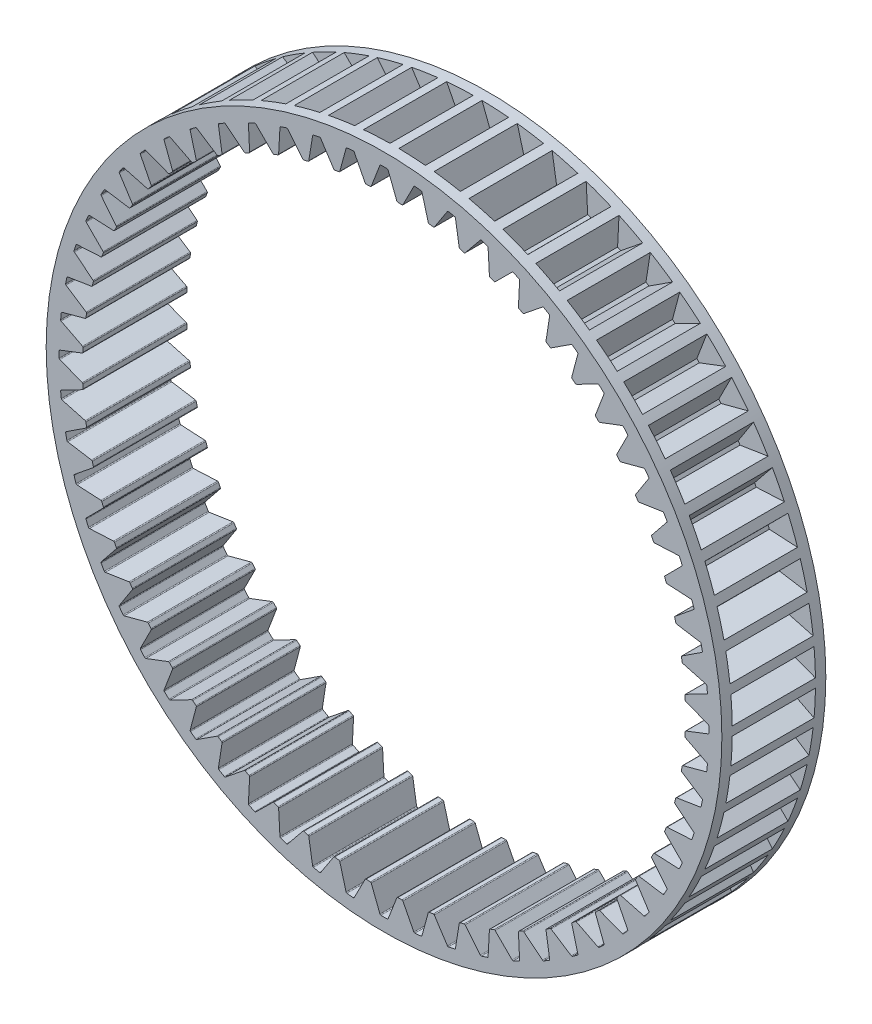
SolidWorks part; units mm, degrees
ref_plane "Front Plane" through (0, 0, 0) normal (0, 0, 1) x (1, 0, 0)
ref_plane "Top Plane" through (0, 0, 0) normal (0, 1, 0) x (1, 0, 0)
ref_plane "Right Plane" through (0, 0, 0) normal (1, 0, 0) x (0, 0, -1)
sketch "Sketch1" plane through (0, 0, 0) normal (0, 0, 1) x (1, 0, 0)
  line L0 (0, 0) -> (0, 31.25) construction
  line L1 (-1.2264, 29.034) -> (-0.3944, 31.1846)
  line L2 (1.2264, 29.034) -> (0.3944, 31.1846)
  line L3 (1.8152, 29.0031) -> (2.8674, 31.055)
  line L4 (4.2546, 28.7467) -> (3.6519, 30.9726)
  line L5 (4.8369, 28.6545) -> (6.0979, 30.5852)
  line L6 (7.2361, 28.1445) -> (6.8694, 30.4212)
  line L7 (7.8056, 27.9919) -> (9.2615, 29.7802)
  line L8 (10.1384, 27.234) -> (10.0117, 29.5365)
  line L9 (10.6888, 27.0227) -> (12.3236, 28.649)
  line L10 (12.9296, 26.025) -> (13.0442, 28.3282)
  line L11 (13.4549, 25.7574) -> (15.2507, 27.2039)
  line L12 (15.5791, 24.531) -> (15.9339, 26.8095)
  line L13 (16.0735, 24.2099) -> (18.0108, 25.4607)
  line L14 (18.0579, 22.7681) -> (18.6489, 24.9971)
  line L15 (18.5161, 22.3971) -> (20.5735, 23.4386)
  line L16 (20.3389, 20.7558) -> (21.1597, 22.9108)
  line L17 (20.7558, 20.3389) -> (22.9108, 21.1597)
  line L18 (22.3971, 18.5161) -> (23.4386, 20.5735)
  line L19 (22.7681, 18.0579) -> (24.9971, 18.6489)
  line L20 (24.2099, 16.0735) -> (25.4607, 18.0108)
  line L21 (24.531, 15.5791) -> (26.8095, 15.9339)
  line L22 (25.7574, 13.4549) -> (27.2039, 15.2507)
  line L23 (26.025, 12.9296) -> (28.3282, 13.0442)
  line L24 (27.0227, 10.6888) -> (28.649, 12.3236)
  line L25 (27.234, 10.1384) -> (29.5365, 10.0117)
  line L26 (27.9919, 7.8056) -> (29.7802, 9.2615)
  line L27 (28.1445, 7.2361) -> (30.4212, 6.8694)
  line L28 (28.6545, 4.8369) -> (30.5852, 6.0979)
  line L29 (28.7467, 4.2546) -> (30.9726, 3.6519)
  line L30 (29.0031, 1.8152) -> (31.055, 2.8674)
  line L31 (29.034, 1.2264) -> (31.1846, 0.3944)
  line L32 (29.034, -1.2264) -> (31.1846, -0.3944)
  line L33 (29.0031, -1.8152) -> (31.055, -2.8674)
  line L34 (28.7467, -4.2546) -> (30.9726, -3.6519)
  line L35 (28.6545, -4.8369) -> (30.5852, -6.0979)
  line L36 (28.1445, -7.2361) -> (30.4212, -6.8694)
  line L37 (27.9919, -7.8056) -> (29.7802, -9.2615)
  line L38 (27.234, -10.1384) -> (29.5365, -10.0117)
  line L39 (27.0227, -10.6888) -> (28.649, -12.3236)
  line L40 (26.025, -12.9296) -> (28.3282, -13.0442)
  line L41 (25.7574, -13.4549) -> (27.2039, -15.2507)
  line L42 (24.531, -15.5791) -> (26.8095, -15.9339)
  line L43 (24.2099, -16.0735) -> (25.4607, -18.0108)
  line L44 (22.7681, -18.0579) -> (24.9971, -18.6489)
  line L45 (22.3971, -18.5161) -> (23.4386, -20.5735)
  line L46 (20.7558, -20.3389) -> (22.9108, -21.1597)
  line L47 (20.3389, -20.7558) -> (21.1597, -22.9108)
  line L48 (18.5161, -22.3971) -> (20.5735, -23.4386)
  line L49 (18.0579, -22.7681) -> (18.6489, -24.9971)
  line L50 (16.0735, -24.2099) -> (18.0108, -25.4607)
  line L51 (15.5791, -24.531) -> (15.9339, -26.8095)
  line L52 (13.4549, -25.7574) -> (15.2507, -27.2039)
  line L53 (12.9296, -26.025) -> (13.0442, -28.3282)
  line L54 (10.6888, -27.0227) -> (12.3236, -28.649)
  line L55 (10.1384, -27.234) -> (10.0117, -29.5365)
  line L56 (7.8056, -27.9919) -> (9.2615, -29.7802)
  line L57 (7.2361, -28.1445) -> (6.8694, -30.4212)
  line L58 (4.8369, -28.6545) -> (6.0979, -30.5852)
  line L59 (4.2546, -28.7467) -> (3.6519, -30.9726)
  line L60 (1.8152, -29.0031) -> (2.8674, -31.055)
  line L61 (1.2264, -29.034) -> (0.3944, -31.1846)
  line L62 (-1.2264, -29.034) -> (-0.3944, -31.1846)
  line L63 (-1.8152, -29.0031) -> (-2.8674, -31.055)
  line L64 (-4.2546, -28.7467) -> (-3.6519, -30.9726)
  line L65 (-4.8369, -28.6545) -> (-6.0979, -30.5852)
  line L66 (-7.2361, -28.1445) -> (-6.8694, -30.4212)
  line L67 (-7.8056, -27.9919) -> (-9.2615, -29.7802)
  line L68 (-10.1384, -27.234) -> (-10.0117, -29.5365)
  line L69 (-10.6888, -27.0227) -> (-12.3236, -28.649)
  line L70 (-12.9296, -26.025) -> (-13.0442, -28.3282)
  line L71 (-13.4549, -25.7574) -> (-15.2507, -27.2039)
  line L72 (-15.5791, -24.531) -> (-15.9339, -26.8095)
  line L73 (-16.0735, -24.2099) -> (-18.0108, -25.4607)
  line L74 (-18.0579, -22.7681) -> (-18.6489, -24.9971)
  line L75 (-18.5161, -22.3971) -> (-20.5735, -23.4386)
  line L76 (-20.3389, -20.7558) -> (-21.1597, -22.9108)
  line L77 (-20.7558, -20.3389) -> (-22.9108, -21.1597)
  line L78 (-22.3971, -18.5161) -> (-23.4386, -20.5735)
  line L79 (-22.7681, -18.0579) -> (-24.9971, -18.6489)
  line L80 (-24.2099, -16.0735) -> (-25.4607, -18.0108)
  line L81 (-24.531, -15.5791) -> (-26.8095, -15.9339)
  line L82 (-25.7574, -13.4549) -> (-27.2039, -15.2507)
  line L83 (-26.025, -12.9296) -> (-28.3282, -13.0442)
  line L84 (-27.0227, -10.6888) -> (-28.649, -12.3236)
  line L85 (-27.234, -10.1384) -> (-29.5365, -10.0117)
  line L86 (-27.9919, -7.8056) -> (-29.7802, -9.2615)
  line L87 (-28.1445, -7.2361) -> (-30.4212, -6.8694)
  line L88 (-28.6545, -4.8369) -> (-30.5852, -6.0979)
  line L89 (-28.7467, -4.2546) -> (-30.9726, -3.6519)
  line L90 (-29.0031, -1.8152) -> (-31.055, -2.8674)
  line L91 (-29.034, -1.2264) -> (-31.1846, -0.3944)
  line L92 (-29.034, 1.2264) -> (-31.1846, 0.3944)
  line L93 (-29.0031, 1.8152) -> (-31.055, 2.8674)
  line L94 (-28.7467, 4.2546) -> (-30.9726, 3.6519)
  line L95 (-28.6545, 4.8369) -> (-30.5852, 6.0979)
  line L96 (-28.1445, 7.2361) -> (-30.4212, 6.8694)
  line L97 (-27.9919, 7.8056) -> (-29.7802, 9.2615)
  line L98 (-27.234, 10.1384) -> (-29.5365, 10.0117)
  line L99 (-27.0227, 10.6888) -> (-28.649, 12.3236)
  line L100 (-26.025, 12.9296) -> (-28.3282, 13.0442)
  line L101 (-25.7574, 13.4549) -> (-27.2039, 15.2507)
  line L102 (-24.531, 15.5791) -> (-26.8095, 15.9339)
  line L103 (-24.2099, 16.0735) -> (-25.4607, 18.0108)
  line L104 (-22.7681, 18.0579) -> (-24.9971, 18.6489)
  line L105 (-22.3971, 18.5161) -> (-23.4386, 20.5735)
  line L106 (-20.7558, 20.3389) -> (-22.9108, 21.1597)
  line L107 (-20.3389, 20.7558) -> (-21.1597, 22.9108)
  line L108 (-18.5161, 22.3971) -> (-20.5735, 23.4386)
  line L109 (-18.0579, 22.7681) -> (-18.6489, 24.9971)
  line L110 (-16.0735, 24.2099) -> (-18.0108, 25.4607)
  line L111 (-15.5791, 24.531) -> (-15.9339, 26.8095)
  line L112 (-13.4549, 25.7574) -> (-15.2507, 27.2039)
  line L113 (-12.9296, 26.025) -> (-13.0442, 28.3282)
  line L114 (-10.6888, 27.0227) -> (-12.3236, 28.649)
  line L115 (-10.1384, 27.234) -> (-10.0117, 29.5365)
  line L116 (-7.8056, 27.9919) -> (-9.2615, 29.7802)
  line L117 (-7.2361, 28.1445) -> (-6.8694, 30.4212)
  line L118 (-4.8369, 28.6545) -> (-6.0979, 30.5852)
  line L119 (-4.2546, 28.7467) -> (-3.6519, 30.9726)
  line L120 (-1.8152, 29.0031) -> (-2.8674, 31.055)
  arc A1 (-1.3152, 28.9702) -> (-1.7203, 28.9489) centre (0, 0) ccw
  arc A2 (0.3021, 31.2485) -> (-0.3021, 31.2485) centre (0, 0) ccw
  circle A3 centre (0, 0) radius 32.5
  arc A4 (-1.2264, 29.034) -> (-1.3152, 28.9702) centre (-1.3197, 29.0701) cw
  arc A5 (1.2264, 29.034) -> (1.3152, 28.9702) centre (1.3197, 29.0701) ccw
  arc A6 (0.3944, 31.1846) -> (0.3021, 31.2485) centre (0.3011, 31.1485) ccw
  arc A7 (-0.3944, 31.1846) -> (-0.3021, 31.2485) centre (-0.3011, 31.1485) cw
  arc A8 (3.5668, 31.0458) -> (2.9659, 31.1089) centre (0, 0) ccw
  arc A9 (2.8674, 31.055) -> (2.9659, 31.1089) centre (2.9564, 31.0094) cw
  arc A10 (3.6519, 30.9726) -> (3.5668, 31.0458) centre (3.5554, 30.9464) ccw
  arc A11 (1.8152, 29.0031) -> (1.7203, 28.9489) centre (1.7262, 29.0488) cw
  arc A12 (4.2546, 28.7467) -> (4.3362, 28.674) centre (4.3511, 28.7729) ccw
  arc A13 (6.7924, 30.5029) -> (6.2014, 30.6285) centre (0, 0) ccw
  arc A14 (6.0979, 30.5852) -> (6.2014, 30.6285) centre (6.1816, 30.5305) cw
  arc A15 (6.8694, 30.4212) -> (6.7924, 30.5029) centre (6.7707, 30.4053) ccw
  arc A16 (4.8369, 28.6545) -> (4.7368, 28.6105) centre (4.7532, 28.7092) cw
  arc A17 (7.2361, 28.1445) -> (7.3097, 28.0637) centre (7.3349, 28.1604) ccw
  arc A18 (9.9437, 29.6258) -> (9.369, 29.8125) centre (0, 0) ccw
  arc A19 (9.2615, 29.7802) -> (9.369, 29.8125) centre (9.339, 29.7171) cw
  arc A20 (10.0117, 29.5365) -> (9.9437, 29.6258) centre (9.9118, 29.531) ccw
  arc A21 (7.8056, 27.9919) -> (7.7015, 27.9587) centre (7.728, 28.0551) cw
  arc A22 (10.1384, 27.234) -> (10.2031, 27.1459) centre (10.2382, 27.2395) ccw
  arc A23 (12.9859, 28.4241) -> (12.4339, 28.6698) centre (0, 0) ccw
  arc A24 (12.3236, 28.649) -> (12.4339, 28.6698) centre (12.3941, 28.5781) cw
  arc A25 (13.0442, 28.3282) -> (12.9859, 28.4241) centre (12.9444, 28.3331) ccw
  arc A26 (10.6888, 27.0227) -> (10.5818, 27.0005) centre (10.6183, 27.0936) cw
  arc A27 (12.9296, 26.025) -> (12.9847, 25.9306) centre (13.0295, 26.0201) ccw
  arc A28 (15.8859, 26.911) -> (15.3626, 27.2131) centre (0, 0) ccw
  arc A29 (15.2507, 27.2039) -> (15.3626, 27.2131) centre (15.3135, 27.126) cw
  arc A30 (15.9339, 26.8095) -> (15.8859, 26.911) centre (15.8351, 26.8249) ccw
  arc A31 (13.4549, 25.7574) -> (13.3461, 25.7465) centre (13.3921, 25.8353) cw
  arc A32 (15.5791, 24.531) -> (15.624, 24.4313) centre (15.6779, 24.5156) ccw
  arc A33 (18.6118, 25.103) -> (18.123, 25.4582) centre (0, 0) ccw
  arc A34 (18.0108, 25.4607) -> (18.123, 25.4582) centre (18.065, 25.3767) cw
  arc A35 (18.6489, 24.9971) -> (18.6118, 25.103) centre (18.5523, 25.0227) ccw
  arc A36 (16.0735, 24.2099) -> (15.9643, 24.2104) centre (16.0193, 24.2939) cw
  arc A37 (18.0579, 22.7681) -> (18.0922, 22.6643) centre (18.1546, 22.7425) ccw
  arc A38 (21.1339, 23.02) -> (20.6848, 23.4243) centre (0, 0) ccw
  arc A39 (20.5735, 23.4386) -> (20.6848, 23.4243) centre (20.6187, 23.3494) cw
  arc A40 (21.1597, 22.9108) -> (21.1339, 23.02) centre (21.0662, 22.9464) ccw
  arc A41 (18.5161, 22.3971) -> (18.4075, 22.409) centre (18.4709, 22.4863) cw
  arc A42 (20.3389, 20.7558) -> (20.3622, 20.649) centre (20.4324, 20.7202) ccw
  arc A43 (23.4243, 20.6848) -> (23.02, 21.1339) centre (0, 0) ccw
  arc A44 (22.9108, 21.1597) -> (23.02, 21.1339) centre (22.9464, 21.0662) cw
  arc A45 (23.4386, 20.5735) -> (23.4243, 20.6848) centre (23.3494, 20.6187) ccw
  arc A46 (20.7558, 20.3389) -> (20.649, 20.3622) centre (20.7202, 20.4324) cw
  arc A47 (22.3971, 18.5161) -> (22.409, 18.4075) centre (22.4863, 18.4709) ccw
  arc A48 (25.4582, 18.123) -> (25.103, 18.6118) centre (0, 0) ccw
  arc A49 (24.9971, 18.6489) -> (25.103, 18.6118) centre (25.0227, 18.5523) cw
  arc A50 (25.4607, 18.0108) -> (25.4582, 18.123) centre (25.3767, 18.065) ccw
  arc A51 (22.7681, 18.0579) -> (22.6643, 18.0922) centre (22.7425, 18.1546) cw
  arc A52 (24.2099, 16.0735) -> (24.2104, 15.9643) centre (24.2939, 16.0193) ccw
  arc A53 (27.2131, 15.3626) -> (26.911, 15.8859) centre (0, 0) ccw
  arc A54 (26.8095, 15.9339) -> (26.911, 15.8859) centre (26.8249, 15.8351) cw
  arc A55 (27.2039, 15.2507) -> (27.2131, 15.3626) centre (27.126, 15.3135) ccw
  arc A56 (24.531, 15.5791) -> (24.4313, 15.624) centre (24.5156, 15.6779) cw
  arc A57 (25.7574, 13.4549) -> (25.7465, 13.3461) centre (25.8353, 13.3921) ccw
  arc A58 (28.6698, 12.4339) -> (28.4241, 12.9859) centre (0, 0) ccw
  arc A59 (28.3282, 13.0442) -> (28.4241, 12.9859) centre (28.3331, 12.9444) cw
  arc A60 (28.649, 12.3236) -> (28.6698, 12.4339) centre (28.5781, 12.3941) ccw
  arc A61 (26.025, 12.9296) -> (25.9306, 12.9847) centre (26.0201, 13.0295) cw
  arc A62 (27.0227, 10.6888) -> (27.0005, 10.5818) centre (27.0936, 10.6183) ccw
  arc A63 (29.8125, 9.369) -> (29.6258, 9.9437) centre (0, 0) ccw
  arc A64 (29.5365, 10.0117) -> (29.6258, 9.9437) centre (29.531, 9.9118) cw
  arc A65 (29.7802, 9.2615) -> (29.8125, 9.369) centre (29.7171, 9.339) ccw
  arc A66 (27.234, 10.1384) -> (27.1459, 10.2031) centre (27.2395, 10.2382) cw
  arc A67 (27.9919, 7.8056) -> (27.9587, 7.7015) centre (28.0551, 7.728) ccw
  arc A68 (30.6285, 6.2014) -> (30.5029, 6.7924) centre (0, 0) ccw
  arc A69 (30.4212, 6.8694) -> (30.5029, 6.7924) centre (30.4053, 6.7707) cw
  arc A70 (30.5852, 6.0979) -> (30.6285, 6.2014) centre (30.5305, 6.1816) ccw
  arc A71 (28.1445, 7.2361) -> (28.0637, 7.3097) centre (28.1604, 7.3349) cw
  arc A72 (28.6545, 4.8369) -> (28.6105, 4.7368) centre (28.7092, 4.7532) ccw
  arc A73 (31.1089, 2.9659) -> (31.0458, 3.5668) centre (0, 0) ccw
  arc A74 (30.9726, 3.6519) -> (31.0458, 3.5668) centre (30.9464, 3.5554) cw
  arc A75 (31.055, 2.8674) -> (31.1089, 2.9659) centre (31.0094, 2.9564) ccw
  arc A76 (28.7467, 4.2546) -> (28.674, 4.3362) centre (28.7729, 4.3511) cw
  arc A77 (29.0031, 1.8152) -> (28.9489, 1.7203) centre (29.0488, 1.7262) ccw
  arc A78 (31.2485, -0.3021) -> (31.2485, 0.3021) centre (0, 0) ccw
  arc A79 (31.1846, 0.3944) -> (31.2485, 0.3021) centre (31.1485, 0.3011) cw
  arc A80 (31.1846, -0.3944) -> (31.2485, -0.3021) centre (31.1485, -0.3011) ccw
  arc A81 (29.034, 1.2264) -> (28.9702, 1.3152) centre (29.0701, 1.3197) cw
  arc A82 (29.034, -1.2264) -> (28.9702, -1.3152) centre (29.0701, -1.3197) ccw
  arc A83 (31.0458, -3.5668) -> (31.1089, -2.9659) centre (0, 0) ccw
  arc A84 (31.055, -2.8674) -> (31.1089, -2.9659) centre (31.0094, -2.9564) cw
  arc A85 (30.9726, -3.6519) -> (31.0458, -3.5668) centre (30.9464, -3.5554) ccw
  arc A86 (29.0031, -1.8152) -> (28.9489, -1.7203) centre (29.0488, -1.7262) cw
  arc A87 (28.7467, -4.2546) -> (28.674, -4.3362) centre (28.7729, -4.3511) ccw
  arc A88 (30.5029, -6.7924) -> (30.6285, -6.2014) centre (0, 0) ccw
  arc A89 (30.5852, -6.0979) -> (30.6285, -6.2014) centre (30.5305, -6.1816) cw
  arc A90 (30.4212, -6.8694) -> (30.5029, -6.7924) centre (30.4053, -6.7707) ccw
  arc A91 (28.6545, -4.8369) -> (28.6105, -4.7368) centre (28.7092, -4.7532) cw
  arc A92 (28.1445, -7.2361) -> (28.0637, -7.3097) centre (28.1604, -7.3349) ccw
  arc A93 (29.6258, -9.9437) -> (29.8125, -9.369) centre (0, 0) ccw
  arc A94 (29.7802, -9.2615) -> (29.8125, -9.369) centre (29.7171, -9.339) cw
  arc A95 (29.5365, -10.0117) -> (29.6258, -9.9437) centre (29.531, -9.9118) ccw
  arc A96 (27.9919, -7.8056) -> (27.9587, -7.7015) centre (28.0551, -7.728) cw
  arc A97 (27.234, -10.1384) -> (27.1459, -10.2031) centre (27.2395, -10.2382) ccw
  arc A98 (28.4241, -12.9859) -> (28.6698, -12.4339) centre (0, 0) ccw
  arc A99 (28.649, -12.3236) -> (28.6698, -12.4339) centre (28.5781, -12.3941) cw
  arc A100 (28.3282, -13.0442) -> (28.4241, -12.9859) centre (28.3331, -12.9444) ccw
  arc A101 (27.0227, -10.6888) -> (27.0005, -10.5818) centre (27.0936, -10.6183) cw
  arc A102 (26.025, -12.9296) -> (25.9306, -12.9847) centre (26.0201, -13.0295) ccw
  arc A103 (26.911, -15.8859) -> (27.2131, -15.3626) centre (0, 0) ccw
  arc A104 (27.2039, -15.2507) -> (27.2131, -15.3626) centre (27.126, -15.3135) cw
  arc A105 (26.8095, -15.9339) -> (26.911, -15.8859) centre (26.8249, -15.8351) ccw
  arc A106 (25.7574, -13.4549) -> (25.7465, -13.3461) centre (25.8353, -13.3921) cw
  arc A107 (24.531, -15.5791) -> (24.4313, -15.624) centre (24.5156, -15.6779) ccw
  arc A108 (25.103, -18.6118) -> (25.4582, -18.123) centre (0, 0) ccw
  arc A109 (25.4607, -18.0108) -> (25.4582, -18.123) centre (25.3767, -18.065) cw
  arc A110 (24.9971, -18.6489) -> (25.103, -18.6118) centre (25.0227, -18.5523) ccw
  arc A111 (24.2099, -16.0735) -> (24.2104, -15.9643) centre (24.2939, -16.0193) cw
  arc A112 (22.7681, -18.0579) -> (22.6643, -18.0922) centre (22.7425, -18.1546) ccw
  arc A113 (23.02, -21.1339) -> (23.4243, -20.6848) centre (0, 0) ccw
  arc A114 (23.4386, -20.5735) -> (23.4243, -20.6848) centre (23.3494, -20.6187) cw
  arc A115 (22.9108, -21.1597) -> (23.02, -21.1339) centre (22.9464, -21.0662) ccw
  arc A116 (22.3971, -18.5161) -> (22.409, -18.4075) centre (22.4863, -18.4709) cw
  arc A117 (20.7558, -20.3389) -> (20.649, -20.3622) centre (20.7202, -20.4324) ccw
  arc A118 (20.6848, -23.4243) -> (21.1339, -23.02) centre (0, 0) ccw
  arc A119 (21.1597, -22.9108) -> (21.1339, -23.02) centre (21.0662, -22.9464) cw
  arc A120 (20.5735, -23.4386) -> (20.6848, -23.4243) centre (20.6187, -23.3494) ccw
  arc A121 (20.3389, -20.7558) -> (20.3622, -20.649) centre (20.4324, -20.7202) cw
  arc A122 (18.5161, -22.3971) -> (18.4075, -22.409) centre (18.4709, -22.4863) ccw
  arc A123 (18.123, -25.4582) -> (18.6118, -25.103) centre (0, 0) ccw
  arc A124 (18.6489, -24.9971) -> (18.6118, -25.103) centre (18.5523, -25.0227) cw
  arc A125 (18.0108, -25.4607) -> (18.123, -25.4582) centre (18.065, -25.3767) ccw
  arc A126 (18.0579, -22.7681) -> (18.0922, -22.6643) centre (18.1546, -22.7425) cw
  arc A127 (16.0735, -24.2099) -> (15.9643, -24.2104) centre (16.0193, -24.2939) ccw
  arc A128 (15.3626, -27.2131) -> (15.8859, -26.911) centre (0, 0) ccw
  arc A129 (15.9339, -26.8095) -> (15.8859, -26.911) centre (15.8351, -26.8249) cw
  arc A130 (15.2507, -27.2039) -> (15.3626, -27.2131) centre (15.3135, -27.126) ccw
  arc A131 (15.5791, -24.531) -> (15.624, -24.4313) centre (15.6779, -24.5156) cw
  arc A132 (13.4549, -25.7574) -> (13.3461, -25.7465) centre (13.3921, -25.8353) ccw
  arc A133 (12.4339, -28.6698) -> (12.9859, -28.4241) centre (0, 0) ccw
  arc A134 (13.0442, -28.3282) -> (12.9859, -28.4241) centre (12.9444, -28.3331) cw
  arc A135 (12.3236, -28.649) -> (12.4339, -28.6698) centre (12.3941, -28.5781) ccw
  arc A136 (12.9296, -26.025) -> (12.9847, -25.9306) centre (13.0295, -26.0201) cw
  arc A137 (10.6888, -27.0227) -> (10.5818, -27.0005) centre (10.6183, -27.0936) ccw
  arc A138 (9.369, -29.8125) -> (9.9437, -29.6258) centre (0, 0) ccw
  arc A139 (10.0117, -29.5365) -> (9.9437, -29.6258) centre (9.9118, -29.531) cw
  arc A140 (9.2615, -29.7802) -> (9.369, -29.8125) centre (9.339, -29.7171) ccw
  arc A141 (10.1384, -27.234) -> (10.2031, -27.1459) centre (10.2382, -27.2395) cw
  arc A142 (7.8056, -27.9919) -> (7.7015, -27.9587) centre (7.728, -28.0551) ccw
  arc A143 (6.2014, -30.6285) -> (6.7924, -30.5029) centre (0, 0) ccw
  arc A144 (6.8694, -30.4212) -> (6.7924, -30.5029) centre (6.7707, -30.4053) cw
  arc A145 (6.0979, -30.5852) -> (6.2014, -30.6285) centre (6.1816, -30.5305) ccw
  arc A146 (7.2361, -28.1445) -> (7.3097, -28.0637) centre (7.3349, -28.1604) cw
  arc A147 (4.8369, -28.6545) -> (4.7368, -28.6105) centre (4.7532, -28.7092) ccw
  arc A148 (2.9659, -31.1089) -> (3.5668, -31.0458) centre (0, 0) ccw
  arc A149 (3.6519, -30.9726) -> (3.5668, -31.0458) centre (3.5554, -30.9464) cw
  arc A150 (2.8674, -31.055) -> (2.9659, -31.1089) centre (2.9564, -31.0094) ccw
  arc A151 (4.2546, -28.7467) -> (4.3362, -28.674) centre (4.3511, -28.7729) cw
  arc A152 (1.8152, -29.0031) -> (1.7203, -28.9489) centre (1.7262, -29.0488) ccw
  arc A153 (-0.3021, -31.2485) -> (0.3021, -31.2485) centre (0, 0) ccw
  arc A154 (0.3944, -31.1846) -> (0.3021, -31.2485) centre (0.3011, -31.1485) cw
  arc A155 (-0.3944, -31.1846) -> (-0.3021, -31.2485) centre (-0.3011, -31.1485) ccw
  arc A156 (1.2264, -29.034) -> (1.3152, -28.9702) centre (1.3197, -29.0701) cw
  arc A157 (-1.2264, -29.034) -> (-1.3152, -28.9702) centre (-1.3197, -29.0701) ccw
  arc A158 (-3.5668, -31.0458) -> (-2.9659, -31.1089) centre (0, 0) ccw
  arc A159 (-2.8674, -31.055) -> (-2.9659, -31.1089) centre (-2.9564, -31.0094) cw
  arc A160 (-3.6519, -30.9726) -> (-3.5668, -31.0458) centre (-3.5554, -30.9464) ccw
  arc A161 (-1.8152, -29.0031) -> (-1.7203, -28.9489) centre (-1.7262, -29.0488) cw
  arc A162 (-4.2546, -28.7467) -> (-4.3362, -28.674) centre (-4.3511, -28.7729) ccw
  arc A163 (-6.7924, -30.5029) -> (-6.2014, -30.6285) centre (0, 0) ccw
  arc A164 (-6.0979, -30.5852) -> (-6.2014, -30.6285) centre (-6.1816, -30.5305) cw
  arc A165 (-6.8694, -30.4212) -> (-6.7924, -30.5029) centre (-6.7707, -30.4053) ccw
  arc A166 (-4.8369, -28.6545) -> (-4.7368, -28.6105) centre (-4.7532, -28.7092) cw
  arc A167 (-7.2361, -28.1445) -> (-7.3097, -28.0637) centre (-7.3349, -28.1604) ccw
  arc A168 (-9.9437, -29.6258) -> (-9.369, -29.8125) centre (0, 0) ccw
  arc A169 (-9.2615, -29.7802) -> (-9.369, -29.8125) centre (-9.339, -29.7171) cw
  arc A170 (-10.0117, -29.5365) -> (-9.9437, -29.6258) centre (-9.9118, -29.531) ccw
  arc A171 (-7.8056, -27.9919) -> (-7.7015, -27.9587) centre (-7.728, -28.0551) cw
  arc A172 (-10.1384, -27.234) -> (-10.2031, -27.1459) centre (-10.2382, -27.2395) ccw
  arc A173 (-12.9859, -28.4241) -> (-12.4339, -28.6698) centre (0, 0) ccw
  arc A174 (-12.3236, -28.649) -> (-12.4339, -28.6698) centre (-12.3941, -28.5781) cw
  arc A175 (-13.0442, -28.3282) -> (-12.9859, -28.4241) centre (-12.9444, -28.3331) ccw
  arc A176 (-10.6888, -27.0227) -> (-10.5818, -27.0005) centre (-10.6183, -27.0936) cw
  arc A177 (-12.9296, -26.025) -> (-12.9847, -25.9306) centre (-13.0295, -26.0201) ccw
  arc A178 (-15.8859, -26.911) -> (-15.3626, -27.2131) centre (0, 0) ccw
  arc A179 (-15.2507, -27.2039) -> (-15.3626, -27.2131) centre (-15.3135, -27.126) cw
  arc A180 (-15.9339, -26.8095) -> (-15.8859, -26.911) centre (-15.8351, -26.8249) ccw
  arc A181 (-13.4549, -25.7574) -> (-13.3461, -25.7465) centre (-13.3921, -25.8353) cw
  arc A182 (-15.5791, -24.531) -> (-15.624, -24.4313) centre (-15.6779, -24.5156) ccw
  arc A183 (-18.6118, -25.103) -> (-18.123, -25.4582) centre (0, 0) ccw
  arc A184 (-18.0108, -25.4607) -> (-18.123, -25.4582) centre (-18.065, -25.3767) cw
  arc A185 (-18.6489, -24.9971) -> (-18.6118, -25.103) centre (-18.5523, -25.0227) ccw
  arc A186 (-16.0735, -24.2099) -> (-15.9643, -24.2104) centre (-16.0193, -24.2939) cw
  arc A187 (-18.0579, -22.7681) -> (-18.0922, -22.6643) centre (-18.1546, -22.7425) ccw
  arc A188 (-21.1339, -23.02) -> (-20.6848, -23.4243) centre (0, 0) ccw
  arc A189 (-20.5735, -23.4386) -> (-20.6848, -23.4243) centre (-20.6187, -23.3494) cw
  arc A190 (-21.1597, -22.9108) -> (-21.1339, -23.02) centre (-21.0662, -22.9464) ccw
  arc A191 (-18.5161, -22.3971) -> (-18.4075, -22.409) centre (-18.4709, -22.4863) cw
  arc A192 (-20.3389, -20.7558) -> (-20.3622, -20.649) centre (-20.4324, -20.7202) ccw
  arc A193 (-23.4243, -20.6848) -> (-23.02, -21.1339) centre (0, 0) ccw
  arc A194 (-22.9108, -21.1597) -> (-23.02, -21.1339) centre (-22.9464, -21.0662) cw
  arc A195 (-23.4386, -20.5735) -> (-23.4243, -20.6848) centre (-23.3494, -20.6187) ccw
  arc A196 (-20.7558, -20.3389) -> (-20.649, -20.3622) centre (-20.7202, -20.4324) cw
  arc A197 (-22.3971, -18.5161) -> (-22.409, -18.4075) centre (-22.4863, -18.4709) ccw
  arc A198 (-25.4582, -18.123) -> (-25.103, -18.6118) centre (0, 0) ccw
  arc A199 (-24.9971, -18.6489) -> (-25.103, -18.6118) centre (-25.0227, -18.5523) cw
  arc A200 (-25.4607, -18.0108) -> (-25.4582, -18.123) centre (-25.3767, -18.065) ccw
  arc A201 (-22.7681, -18.0579) -> (-22.6643, -18.0922) centre (-22.7425, -18.1546) cw
  arc A202 (-24.2099, -16.0735) -> (-24.2104, -15.9643) centre (-24.2939, -16.0193) ccw
  arc A203 (-27.2131, -15.3626) -> (-26.911, -15.8859) centre (0, 0) ccw
  arc A204 (-26.8095, -15.9339) -> (-26.911, -15.8859) centre (-26.8249, -15.8351) cw
  arc A205 (-27.2039, -15.2507) -> (-27.2131, -15.3626) centre (-27.126, -15.3135) ccw
  arc A206 (-24.531, -15.5791) -> (-24.4313, -15.624) centre (-24.5156, -15.6779) cw
  arc A207 (-25.7574, -13.4549) -> (-25.7465, -13.3461) centre (-25.8353, -13.3921) ccw
  arc A208 (-28.6698, -12.4339) -> (-28.4241, -12.9859) centre (0, 0) ccw
  arc A209 (-28.3282, -13.0442) -> (-28.4241, -12.9859) centre (-28.3331, -12.9444) cw
  arc A210 (-28.649, -12.3236) -> (-28.6698, -12.4339) centre (-28.5781, -12.3941) ccw
  arc A211 (-26.025, -12.9296) -> (-25.9306, -12.9847) centre (-26.0201, -13.0295) cw
  arc A212 (-27.0227, -10.6888) -> (-27.0005, -10.5818) centre (-27.0936, -10.6183) ccw
  arc A213 (-29.8125, -9.369) -> (-29.6258, -9.9437) centre (0, 0) ccw
  arc A214 (-29.5365, -10.0117) -> (-29.6258, -9.9437) centre (-29.531, -9.9118) cw
  arc A215 (-29.7802, -9.2615) -> (-29.8125, -9.369) centre (-29.7171, -9.339) ccw
  arc A216 (-27.234, -10.1384) -> (-27.1459, -10.2031) centre (-27.2395, -10.2382) cw
  arc A217 (-27.9919, -7.8056) -> (-27.9587, -7.7015) centre (-28.0551, -7.728) ccw
  arc A218 (-30.6285, -6.2014) -> (-30.5029, -6.7924) centre (0, 0) ccw
  arc A219 (-30.4212, -6.8694) -> (-30.5029, -6.7924) centre (-30.4053, -6.7707) cw
  arc A220 (-30.5852, -6.0979) -> (-30.6285, -6.2014) centre (-30.5305, -6.1816) ccw
  arc A221 (-28.1445, -7.2361) -> (-28.0637, -7.3097) centre (-28.1604, -7.3349) cw
  arc A222 (-28.6545, -4.8369) -> (-28.6105, -4.7368) centre (-28.7092, -4.7532) ccw
  arc A223 (-31.1089, -2.9659) -> (-31.0458, -3.5668) centre (0, 0) ccw
  arc A224 (-30.9726, -3.6519) -> (-31.0458, -3.5668) centre (-30.9464, -3.5554) cw
  arc A225 (-31.055, -2.8674) -> (-31.1089, -2.9659) centre (-31.0094, -2.9564) ccw
  arc A226 (-28.7467, -4.2546) -> (-28.674, -4.3362) centre (-28.7729, -4.3511) cw
  arc A227 (-29.0031, -1.8152) -> (-28.9489, -1.7203) centre (-29.0488, -1.7262) ccw
  arc A228 (-31.2485, 0.3021) -> (-31.2485, -0.3021) centre (0, 0) ccw
  arc A229 (-31.1846, -0.3944) -> (-31.2485, -0.3021) centre (-31.1485, -0.3011) cw
  arc A230 (-31.1846, 0.3944) -> (-31.2485, 0.3021) centre (-31.1485, 0.3011) ccw
  arc A231 (-29.034, -1.2264) -> (-28.9702, -1.3152) centre (-29.0701, -1.3197) cw
  arc A232 (-29.034, 1.2264) -> (-28.9702, 1.3152) centre (-29.0701, 1.3197) ccw
  arc A233 (-31.0458, 3.5668) -> (-31.1089, 2.9659) centre (0, 0) ccw
  arc A234 (-31.055, 2.8674) -> (-31.1089, 2.9659) centre (-31.0094, 2.9564) cw
  arc A235 (-30.9726, 3.6519) -> (-31.0458, 3.5668) centre (-30.9464, 3.5554) ccw
  arc A236 (-29.0031, 1.8152) -> (-28.9489, 1.7203) centre (-29.0488, 1.7262) cw
  arc A237 (-28.7467, 4.2546) -> (-28.674, 4.3362) centre (-28.7729, 4.3511) ccw
  arc A238 (-30.5029, 6.7924) -> (-30.6285, 6.2014) centre (0, 0) ccw
  arc A239 (-30.5852, 6.0979) -> (-30.6285, 6.2014) centre (-30.5305, 6.1816) cw
  arc A240 (-30.4212, 6.8694) -> (-30.5029, 6.7924) centre (-30.4053, 6.7707) ccw
  arc A241 (-28.6545, 4.8369) -> (-28.6105, 4.7368) centre (-28.7092, 4.7532) cw
  arc A242 (-28.1445, 7.2361) -> (-28.0637, 7.3097) centre (-28.1604, 7.3349) ccw
  arc A243 (-29.6258, 9.9437) -> (-29.8125, 9.369) centre (0, 0) ccw
  arc A244 (-29.7802, 9.2615) -> (-29.8125, 9.369) centre (-29.7171, 9.339) cw
  arc A245 (-29.5365, 10.0117) -> (-29.6258, 9.9437) centre (-29.531, 9.9118) ccw
  arc A246 (-27.9919, 7.8056) -> (-27.9587, 7.7015) centre (-28.0551, 7.728) cw
  arc A247 (-27.234, 10.1384) -> (-27.1459, 10.2031) centre (-27.2395, 10.2382) ccw
  arc A248 (-28.4241, 12.9859) -> (-28.6698, 12.4339) centre (0, 0) ccw
  arc A249 (-28.649, 12.3236) -> (-28.6698, 12.4339) centre (-28.5781, 12.3941) cw
  arc A250 (-28.3282, 13.0442) -> (-28.4241, 12.9859) centre (-28.3331, 12.9444) ccw
  arc A251 (-27.0227, 10.6888) -> (-27.0005, 10.5818) centre (-27.0936, 10.6183) cw
  arc A252 (-26.025, 12.9296) -> (-25.9306, 12.9847) centre (-26.0201, 13.0295) ccw
  arc A253 (-26.911, 15.8859) -> (-27.2131, 15.3626) centre (0, 0) ccw
  arc A254 (-27.2039, 15.2507) -> (-27.2131, 15.3626) centre (-27.126, 15.3135) cw
  arc A255 (-26.8095, 15.9339) -> (-26.911, 15.8859) centre (-26.8249, 15.8351) ccw
  arc A256 (-25.7574, 13.4549) -> (-25.7465, 13.3461) centre (-25.8353, 13.3921) cw
  arc A257 (-24.531, 15.5791) -> (-24.4313, 15.624) centre (-24.5156, 15.6779) ccw
  arc A258 (-25.103, 18.6118) -> (-25.4582, 18.123) centre (0, 0) ccw
  arc A259 (-25.4607, 18.0108) -> (-25.4582, 18.123) centre (-25.3767, 18.065) cw
  arc A260 (-24.9971, 18.6489) -> (-25.103, 18.6118) centre (-25.0227, 18.5523) ccw
  arc A261 (-24.2099, 16.0735) -> (-24.2104, 15.9643) centre (-24.2939, 16.0193) cw
  arc A262 (-22.7681, 18.0579) -> (-22.6643, 18.0922) centre (-22.7425, 18.1546) ccw
  arc A263 (-23.02, 21.1339) -> (-23.4243, 20.6848) centre (0, 0) ccw
  arc A264 (-23.4386, 20.5735) -> (-23.4243, 20.6848) centre (-23.3494, 20.6187) cw
  arc A265 (-22.9108, 21.1597) -> (-23.02, 21.1339) centre (-22.9464, 21.0662) ccw
  arc A266 (-22.3971, 18.5161) -> (-22.409, 18.4075) centre (-22.4863, 18.4709) cw
  arc A267 (-20.7558, 20.3389) -> (-20.649, 20.3622) centre (-20.7202, 20.4324) ccw
  arc A268 (-20.6848, 23.4243) -> (-21.1339, 23.02) centre (0, 0) ccw
  arc A269 (-21.1597, 22.9108) -> (-21.1339, 23.02) centre (-21.0662, 22.9464) cw
  arc A270 (-20.5735, 23.4386) -> (-20.6848, 23.4243) centre (-20.6187, 23.3494) ccw
  arc A271 (-20.3389, 20.7558) -> (-20.3622, 20.649) centre (-20.4324, 20.7202) cw
  arc A272 (-18.5161, 22.3971) -> (-18.4075, 22.409) centre (-18.4709, 22.4863) ccw
  arc A273 (-18.123, 25.4582) -> (-18.6118, 25.103) centre (0, 0) ccw
  arc A274 (-18.6489, 24.9971) -> (-18.6118, 25.103) centre (-18.5523, 25.0227) cw
  arc A275 (-18.0108, 25.4607) -> (-18.123, 25.4582) centre (-18.065, 25.3767) ccw
  arc A276 (-18.0579, 22.7681) -> (-18.0922, 22.6643) centre (-18.1546, 22.7425) cw
  arc A277 (-16.0735, 24.2099) -> (-15.9643, 24.2104) centre (-16.0193, 24.2939) ccw
  arc A278 (-15.3626, 27.2131) -> (-15.8859, 26.911) centre (0, 0) ccw
  arc A279 (-15.9339, 26.8095) -> (-15.8859, 26.911) centre (-15.8351, 26.8249) cw
  arc A280 (-15.2507, 27.2039) -> (-15.3626, 27.2131) centre (-15.3135, 27.126) ccw
  arc A281 (-15.5791, 24.531) -> (-15.624, 24.4313) centre (-15.6779, 24.5156) cw
  arc A282 (-13.4549, 25.7574) -> (-13.3461, 25.7465) centre (-13.3921, 25.8353) ccw
  arc A283 (-12.4339, 28.6698) -> (-12.9859, 28.4241) centre (0, 0) ccw
  arc A284 (-13.0442, 28.3282) -> (-12.9859, 28.4241) centre (-12.9444, 28.3331) cw
  arc A285 (-12.3236, 28.649) -> (-12.4339, 28.6698) centre (-12.3941, 28.5781) ccw
  arc A286 (-12.9296, 26.025) -> (-12.9847, 25.9306) centre (-13.0295, 26.0201) cw
  arc A287 (-10.6888, 27.0227) -> (-10.5818, 27.0005) centre (-10.6183, 27.0936) ccw
  arc A288 (-9.369, 29.8125) -> (-9.9437, 29.6258) centre (0, 0) ccw
  arc A289 (-10.0117, 29.5365) -> (-9.9437, 29.6258) centre (-9.9118, 29.531) cw
  arc A290 (-9.2615, 29.7802) -> (-9.369, 29.8125) centre (-9.339, 29.7171) ccw
  arc A291 (-10.1384, 27.234) -> (-10.2031, 27.1459) centre (-10.2382, 27.2395) cw
  arc A292 (-7.8056, 27.9919) -> (-7.7015, 27.9587) centre (-7.728, 28.0551) ccw
  arc A293 (-6.2014, 30.6285) -> (-6.7924, 30.5029) centre (0, 0) ccw
  arc A294 (-6.8694, 30.4212) -> (-6.7924, 30.5029) centre (-6.7707, 30.4053) cw
  arc A295 (-6.0979, 30.5852) -> (-6.2014, 30.6285) centre (-6.1816, 30.5305) ccw
  arc A296 (-7.2361, 28.1445) -> (-7.3097, 28.0637) centre (-7.3349, 28.1604) cw
  arc A297 (-4.8369, 28.6545) -> (-4.7368, 28.6105) centre (-4.7532, 28.7092) ccw
  arc A298 (-2.9659, 31.1089) -> (-3.5668, 31.0458) centre (0, 0) ccw
  arc A299 (-3.6519, 30.9726) -> (-3.5668, 31.0458) centre (-3.5554, 30.9464) cw
  arc A300 (-2.8674, 31.055) -> (-2.9659, 31.1089) centre (-2.9564, 31.0094) ccw
  arc A301 (-4.2546, 28.7467) -> (-4.3362, 28.674) centre (-4.3511, 28.7729) cw
  arc A302 (-1.8152, 29.0031) -> (-1.7203, 28.9489) centre (-1.7262, 29.0488) ccw
  arc A303 (1.7203, 28.9489) -> (1.3152, 28.9702) centre (0, 0) ccw
  arc A304 (-4.3362, 28.674) -> (-4.7368, 28.6105) centre (0, 0) ccw
  arc A305 (-7.3097, 28.0637) -> (-7.7015, 27.9587) centre (0, 0) ccw
  arc A306 (4.7368, 28.6105) -> (4.3362, 28.674) centre (0, 0) ccw
  arc A307 (7.7015, 27.9587) -> (7.3097, 28.0637) centre (0, 0) ccw
  arc A308 (10.5818, 27.0005) -> (10.2031, 27.1459) centre (0, 0) ccw
  arc A309 (13.3461, 25.7465) -> (12.9847, 25.9306) centre (0, 0) ccw
  arc A310 (-10.2031, 27.1459) -> (-10.5818, 27.0005) centre (0, 0) ccw
  arc A311 (-12.9847, 25.9306) -> (-13.3461, 25.7465) centre (0, 0) ccw
  arc A312 (-15.624, 24.4313) -> (-15.9643, 24.2104) centre (0, 0) ccw
  arc A313 (-18.0922, 22.6643) -> (-18.4075, 22.409) centre (0, 0) ccw
  arc A314 (-20.3622, 20.649) -> (-20.649, 20.3622) centre (0, 0) ccw
  arc A315 (-22.409, 18.4075) -> (-22.6643, 18.0922) centre (0, 0) ccw
  arc A316 (-24.2104, 15.9643) -> (-24.4313, 15.624) centre (0, 0) ccw
  arc A317 (15.9643, 24.2104) -> (15.624, 24.4313) centre (0, 0) ccw
  arc A318 (18.4075, 22.409) -> (18.0922, 22.6643) centre (0, 0) ccw
  arc A319 (20.649, 20.3622) -> (20.3622, 20.649) centre (0, 0) ccw
  arc A320 (22.6643, 18.0922) -> (22.409, 18.4075) centre (0, 0) ccw
  arc A321 (-25.7465, 13.3461) -> (-25.9306, 12.9847) centre (0, 0) ccw
  arc A322 (-27.0005, 10.5818) -> (-27.1459, 10.2031) centre (0, 0) ccw
  arc A323 (-27.9587, 7.7015) -> (-28.0637, 7.3097) centre (0, 0) ccw
  arc A324 (-28.6105, 4.7368) -> (-28.674, 4.3362) centre (0, 0) ccw
  arc A325 (-28.9489, 1.7203) -> (-28.9702, 1.3152) centre (0, 0) ccw
  arc A326 (-28.9702, -1.3152) -> (-28.9489, -1.7203) centre (0, 0) ccw
  arc A327 (-28.674, -4.3362) -> (-28.6105, -4.7368) centre (0, 0) ccw
  arc A328 (-28.0637, -7.3097) -> (-27.9587, -7.7015) centre (0, 0) ccw
  arc A329 (24.4313, 15.624) -> (24.2104, 15.9643) centre (0, 0) ccw
  arc A330 (25.9306, 12.9847) -> (25.7465, 13.3461) centre (0, 0) ccw
  arc A331 (27.1459, 10.2031) -> (27.0005, 10.5818) centre (0, 0) ccw
  arc A332 (28.0637, 7.3097) -> (27.9587, 7.7015) centre (0, 0) ccw
  arc A333 (28.674, 4.3362) -> (28.6105, 4.7368) centre (0, 0) ccw
  arc A334 (28.9702, 1.3152) -> (28.9489, 1.7203) centre (0, 0) ccw
  arc A335 (28.9489, -1.7203) -> (28.9702, -1.3152) centre (0, 0) ccw
  arc A336 (28.6105, -4.7368) -> (28.674, -4.3362) centre (0, 0) ccw
  arc A337 (27.9587, -7.7015) -> (28.0637, -7.3097) centre (0, 0) ccw
  arc A338 (27.0005, -10.5818) -> (27.1459, -10.2031) centre (0, 0) ccw
  arc A339 (25.7465, -13.3461) -> (25.9306, -12.9847) centre (0, 0) ccw
  arc A340 (-27.1459, -10.2031) -> (-27.0005, -10.5818) centre (0, 0) ccw
  arc A341 (-25.9306, -12.9847) -> (-25.7465, -13.3461) centre (0, 0) ccw
  arc A342 (-24.4313, -15.624) -> (-24.2104, -15.9643) centre (0, 0) ccw
  arc A343 (-22.6643, -18.0922) -> (-22.409, -18.4075) centre (0, 0) ccw
  arc A344 (-20.649, -20.3622) -> (-20.3622, -20.649) centre (0, 0) ccw
  arc A345 (-18.4075, -22.409) -> (-18.0922, -22.6643) centre (0, 0) ccw
  arc A346 (-15.9643, -24.2104) -> (-15.624, -24.4313) centre (0, 0) ccw
  arc A347 (-13.3461, -25.7465) -> (-12.9847, -25.9306) centre (0, 0) ccw
  arc A348 (-10.5818, -27.0005) -> (-10.2031, -27.1459) centre (0, 0) ccw
  arc A349 (-7.7015, -27.9587) -> (-7.3097, -28.0637) centre (0, 0) ccw
  arc A350 (-4.7368, -28.6105) -> (-4.3362, -28.674) centre (0, 0) ccw
  arc A351 (-1.7203, -28.9489) -> (-1.3152, -28.9702) centre (0, 0) ccw
  arc A352 (1.3152, -28.9702) -> (1.7203, -28.9489) centre (0, 0) ccw
  arc A353 (4.3362, -28.674) -> (4.7368, -28.6105) centre (0, 0) ccw
  arc A354 (7.3097, -28.0637) -> (7.7015, -27.9587) centre (0, 0) ccw
  arc A355 (10.2031, -27.1459) -> (10.5818, -27.0005) centre (0, 0) ccw
  arc A356 (12.9847, -25.9306) -> (13.3461, -25.7465) centre (0, 0) ccw
  arc A357 (15.624, -24.4313) -> (15.9643, -24.2104) centre (0, 0) ccw
  arc A358 (18.0922, -22.6643) -> (18.4075, -22.409) centre (0, 0) ccw
  arc A359 (20.3622, -20.649) -> (20.649, -20.3622) centre (0, 0) ccw
  arc A360 (22.409, -18.4075) -> (22.6643, -18.0922) centre (0, 0) ccw
  arc A361 (24.2104, -15.9643) -> (24.4313, -15.624) centre (0, 0) ccw
  point P10 (-1.25, 28.973)
  point P13 (1.25, 28.973)
  point P16 (0.37, 31.2478)
  point P19 (-0.37, 31.2478)
  point P20 (0, 0)
  point P21 (0, 0)
  point P731 (0, 0)
  dimension "D1" = 65
  dimension "D2" = 62.5
  dimension "D3" = 58
  dimension "D6" = 0.1
  dimension "D4" = 21.15
  dimension "D5" = 1.25
  dimension "D7" = 60
extrude "Boss-Extrude1" add sketch "Sketch1" along normal blind 10
ref_plane "Plane1" through (0, 0, 9) normal (0, 0, 1) x (1, 0, 0)
sketch "Sketch8" plane through (0, 0, 9) normal (0, 0, 1) x (1, 0, 0)
  line L0 (0, 0) -> (0, 31.25) construction
  line L1 (-0.5439, 34.9958) -> (1.4015, 29.9672)
  line L2 (1.7386, 29.9496) -> (4.199, 34.7472)
  line L3 (1.2264, 29.034) -> (0.3944, 31.1846) construction
  line L5 (2.8674, 31.055) -> (1.8152, 29.0031) construction
  arc A0 (0.3021, 31.2485) -> (-0.3021, 31.2485) centre (0, 0) ccw construction
  arc A1 (1.7386, 29.9496) -> (1.4015, 29.9672) centre (0, 0) ccw
  arc A4 (4.199, 34.7472) -> (-0.5439, 34.9958) centre (0, 0) ccw
  point P18 (0, 0)
  point P19 (0, 0)
  point P20 (0, 0)
  point P21 (0, 0)
  dimension "D4" = 60
  dimension "D5" = 70
  dimension "D2" = 0.5
  dimension "D3" = 0.5
extrude "Cut-Extrude9" cut sketch "Sketch8" against normal blind 8
pattern_circular "CirPattern2" count 60 over 360 about axis through (0, 0, 0) along (0, 0, 1) of "Cut-Extrude9"
